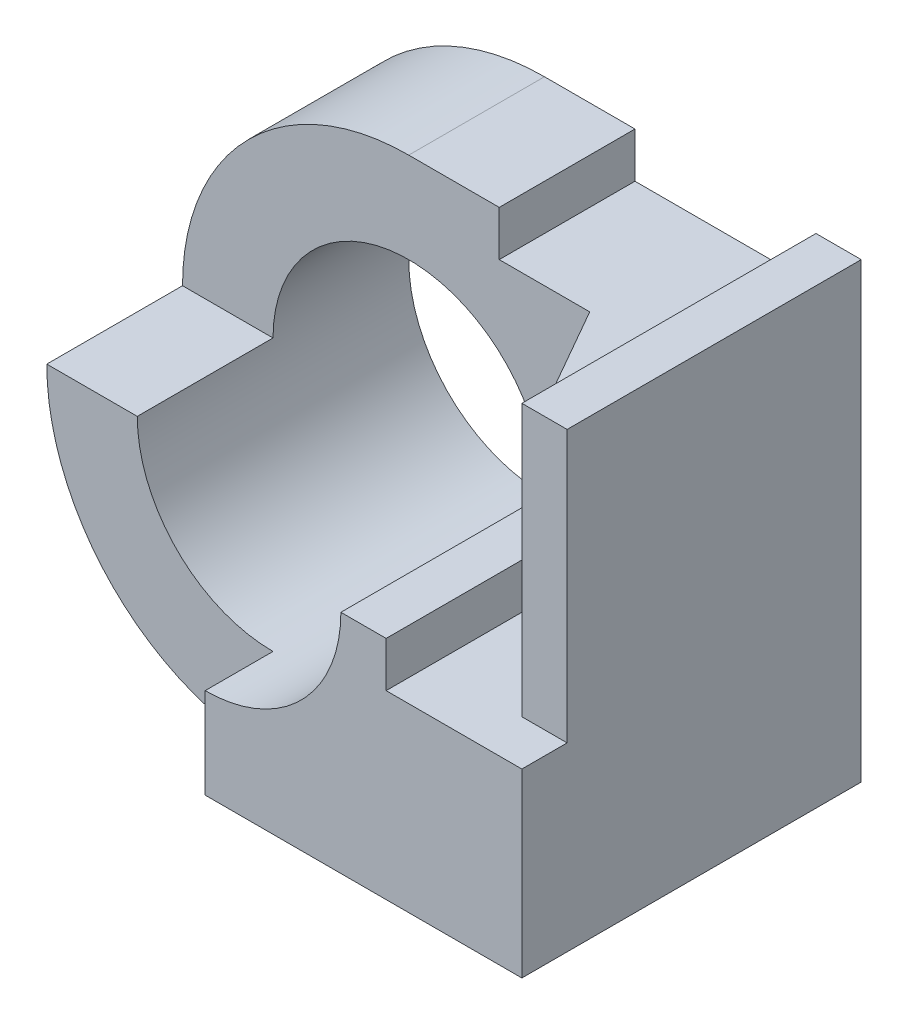
SolidWorks part; units mm, degrees
ref_plane "Front" through (0, 0, 0) normal (0, 0, 1) x (1, 0, 0)
ref_plane "Top" through (0, 0, 0) normal (0, 1, 0) x (1, 0, 0)
ref_plane "Right" through (0, 0, 0) normal (1, 0, 0) x (0, 0, -1)
sketch "Sketch1" plane through (0, 0, 0) normal (0, 0, 1) x (1, 0, 0)
  line L1 (-3.5, -5) -> (3.5, -5)
  line L2 (-3.5, -5) -> (-3.5, 5)
  line L3 (-3.5, 5) -> (3.5, 5)
  line L4 (3.5, -5) -> (3.5, 5)
  line L5 (-3.5, -5) -> (3.5, 5) construction
  line L6 (-3.5, 5) -> (3.5, -5) construction
  line L7 (2.5, 5) -> (-1.5, 5)
  line L8 (2.5, 5) -> (2.5, 4)
  line L9 (2.5, 4) -> (-1.5, 4)
  line L10 (-1.5, 5) -> (-1.5, 4)
  arc A0 (-3.5, 5) -> (-3.5, -5) centre (-3.5, 0) ccw
  circle A1 centre (-3.5, 0) radius 3
  point P0 (0, 0)
  dimension "D3" = 6
  dimension "D1" = 10
  dimension "D2" = 7
  dimension "D4" = 1
  dimension "D5" = 4
  dimension "D6" = 5
extrude "Boss-Extrude1" add sketch "Sketch1" along normal blind 7.5 contours A1 L2 L1 L4 L3 L8 L9 L10 | A1 L2 A0
sketch "Sketch2" plane through (0, 0, 7.5) normal (0, 0, 1) x (1, 0, 0)
  line L1 (-8.5, 0) -> (0.5, 0)
  line L2 (-8.5, 0) -> (-8.5, 5)
  line L3 (-8.5, 5) -> (0.5, 5)
  line L4 (0.5, 0) -> (0.5, 5)
  arc A0 (-3.5, 5) -> (-3.5, -5) centre (-3.5, 0) ccw construction
  dimension "D1" = 9
extrude "Cut-Extrude1" cut sketch "Sketch2" against normal blind 4.5
sketch "Sketch3" plane through (0, 0, 7.5) normal (0, 0, 1) x (1, 0, 0)
  line L1 (-8.5, 0) -> (-3.5, 0)
  line L2 (-8.5, 0) -> (-8.5, -5)
  line L3 (-8.5, -5) -> (-3.5, -5)
  line L4 (-3.5, 0) -> (-3.5, -5)
  arc A0 (-8.5, 0) -> (-3.5, -5) centre (-3.5, 0) ccw construction
extrude "Cut-Extrude2" cut sketch "Sketch3" against normal blind 1.5
sketch "Sketch4" plane through (0, 5, 0) normal (0, 1, 0) x (1, 0, 0)
  line L0 (3.5, -6.5) -> (2.5, -6.5)
  line L1 (3.5, -7.5) -> (3.5, 0) construction
  line L2 (2.5, -7.5) -> (2.5, 0) construction
  line L3 (2.5, -6.5) -> (0.5, -3)
  line L4 (0.5, -3) -> (0.5, -7.5)
  line L5 (0.5, -7.5) -> (3.5, -7.5)
  line L6 (3.5, -7.5) -> (3.5, -6.5)
  dimension "D1" = 1
extrude "Cut-Extrude3" cut sketch "Sketch4" against normal blind 6
